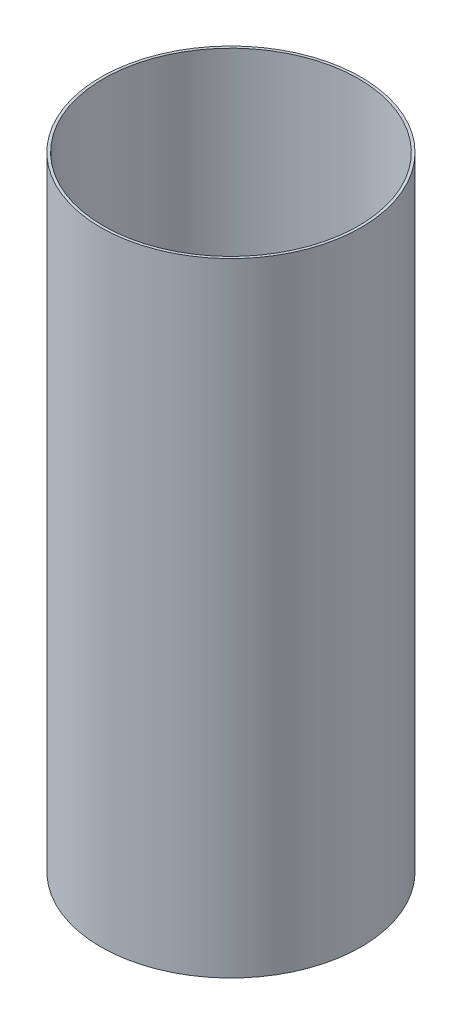
SolidWorks part; units mm, degrees
material "Hexcel AS4C (3000 Filaments)"
ref_plane "Front Plane" through (0, 0, 0) normal (0, 0, 1) x (1, 0, 0)
ref_plane "Top Plane" through (0, 0, 0) normal (0, 1, 0) x (1, 0, 0)
ref_plane "Right Plane" through (0, 0, 0) normal (1, 0, 0) x (0, 0, -1)
sketch "Sketch1" plane through (0, 0, 0) normal (0, 1, 0) x (1, 0, 0)
  circle A0 centre (0, 0) radius 76.2889
  circle A1 centre (0, 0) radius 77.8637
  dimension "D1" = 152.5778
  dimension "D2" = 155.7274
extrude "Boss-Extrude1" add sketch "Sketch1" along normal blind 372.618
